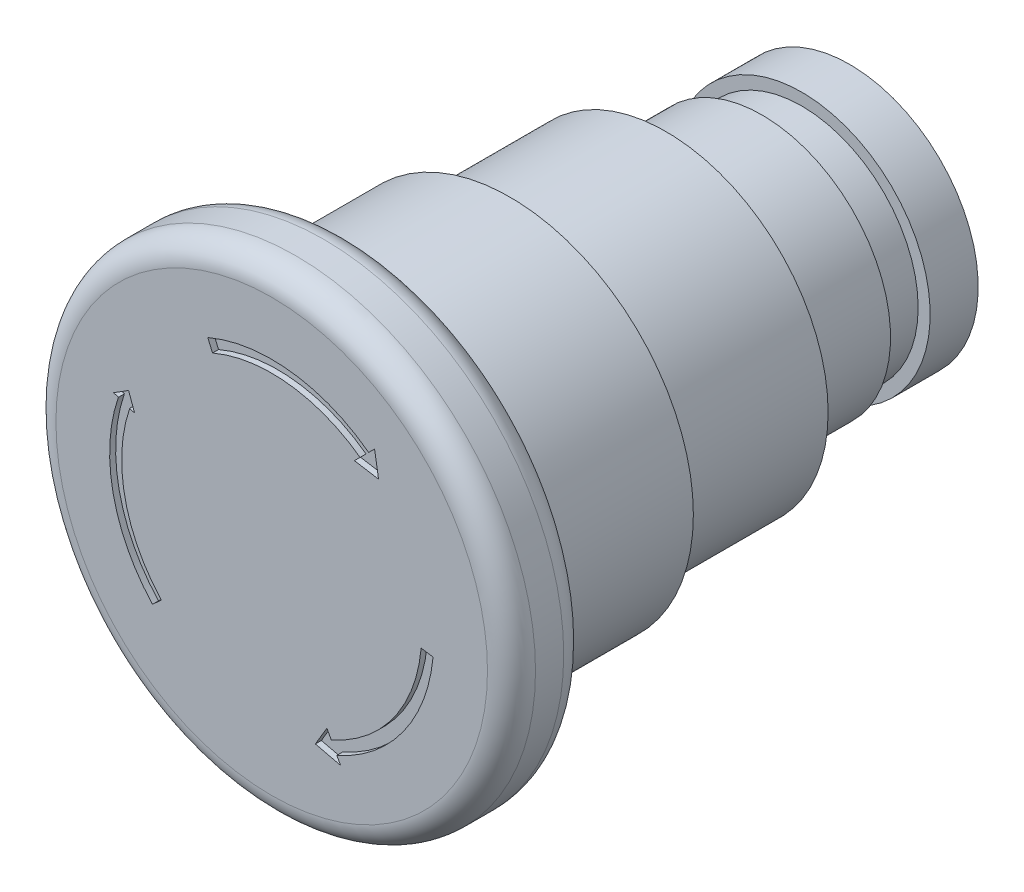
SolidWorks part; units mm, degrees
ref_plane "Front Plane" through (0, 0, 0) normal (0, 0, 1) x (1, 0, 0)
ref_plane "Top Plane" through (0, 0, 0) normal (0, 1, 0) x (1, 0, 0)
ref_plane "Right Plane" through (0, 0, 0) normal (1, 0, 0) x (0, 0, -1)
sketch "Sketch1" plane through (0, 0, 0) normal (0, 0, 1) x (1, 0, 0)
  circle A0 centre (0, 0) radius 19.975
  dimension "D1" = 39.95
extrude "Boss-Extrude1" add sketch "Sketch1" along normal blind 6.35
sketch "Sketch2" plane through (0, 0, 0) normal (0, 0, -1) x (-1, 0, 0)
  circle A0 centre (0, 0) radius 15.275
  dimension "D1" = 30.55
extrude "Boss-Extrude2" add sketch "Sketch2" along normal blind 13.5
sketch "Sketch3" plane through (0, 0, -13.5) normal (0, 0, -1) x (-1, 0, 0)
  circle A0 centre (0, 0) radius 13.5
  dimension "D1" = 27
extrude "Boss-Extrude3" add sketch "Sketch3" along normal blind 13
sketch "Sketch4" plane through (0, 0, -26.5) normal (0, 0, -1) x (-1, 0, 0)
  circle A0 centre (0, 0) radius 10.7
  dimension "D1" = 21.4
extrude "Boss-Extrude4" add sketch "Sketch4" along normal blind 15.3
fillet "Fillet1" radius 2 3 edges at (15.275, 0, 0) (19.975, 0, 0) (19.975, 0, 6.35)
sketch "Sketch6" plane through (0, 0, 0) normal (1, 0, 0) x (0, 0, -1)
  line L0 (37.8, 10.7) -> (34.5, 10.7)
  line L1 (41.8, 10.7) -> (26.5, 10.7) construction
  line L2 (34.5, 10.7) -> (34.5, 9.7)
  line L3 (34.5, 9.7) -> (37.8, 9.7)
  line L4 (37.8, 9.7) -> (37.8, 10.7)
  line L5 (41.8, -10.7) -> (41.8, 10.7) construction
  dimension "D1" = 3.3
  dimension "D2" = 1
  dimension "D3" = 4
revolve "Cut-Revolve1" cut sketch "Sketch6" angle 360 about axis through (0, 0, -41.8) along (0, 0, 1)
sketch "Sketch7" plane through (0, 0, 6.35) normal (0, 0, 1) x (1, 0, 0)
  line L0 (6.8898, 9.6304) -> (7.3617, 10.1022)
  line L1 (6.8898, 9.6304) -> (8.902, 9.2975)
  line L2 (8.902, 9.2975) -> (8.5691, 11.3097)
  line L3 (4.6004, -10.8118) -> (4.9552, -11.4759)
  line L4 (5.7332, -12.9317) -> (3.6382, -12.4325)
  line L5 (3.6382, -12.4325) -> (4.6004, -10.8118)
  line L6 (-13.1681, 4.5051) -> (-12.7731, 4.37)
  line L7 (-11.4167, 3.9059) -> (-11.9226, 5.2864)
  line L8 (-11.9226, 5.2864) -> (-13.1681, 4.5051)
  line L9 (-5.3243, 12.4057) -> (-4.8539, 11.3097)
  line L10 (-9.9308, -9.1449) -> (-9.1952, -8.4675)
  line L11 (12.4505, -1.1109) -> (13.4409, -1.2618)
  line L12 (8.0768, 10.8174) -> (8.5691, 11.3097)
  line L13 (5.428, -12.3607) -> (5.7332, -12.9317)
  line L14 (-11.827, 4.0463) -> (-11.4167, 3.9059)
  arc A0 (-11.827, 4.0463) -> (-9.1952, -8.4675) centre (0, 0) ccw
  arc A1 (-12.7731, 4.37) -> (-9.9308, -9.1449) centre (0, 0) ccw
  circle A2 centre (0, 0) radius 13.5 construction
  circle A3 centre (0, 0) radius 12.5 construction
  arc A4 (4.9552, -11.4759) -> (12.4505, -1.1109) centre (0, 0) ccw
  arc A5 (5.428, -12.3607) -> (13.4409, -1.2618) centre (0, 0) ccw
  arc A6 (7.3617, 10.1022) -> (-4.9299, 11.4868) centre (0, 0) ccw
  arc A7 (8.0768, 10.8174) -> (-5.3243, 12.4057) centre (0, 0) ccw
  dimension "D1" = 25
  dimension "D2" = 1
extrude "Cut-Extrude1" cut sketch "Sketch7" against normal blind 0.5 contours L12 A7 L9 A6 L0 L1 L2 | L13 A5 L11 A4 L3 L5 L4 | A0 L10 A1 L6 L8 L7 L14
